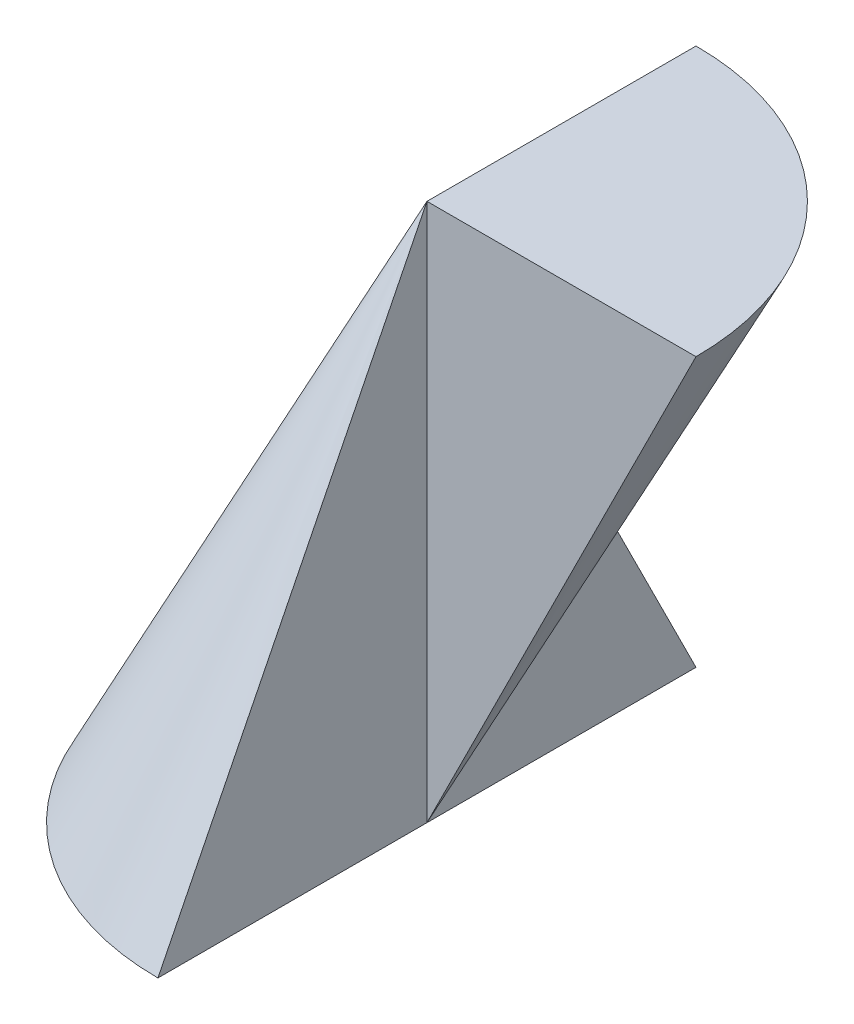
SolidWorks part; units mm, degrees
ref_plane "Front" through (0, 0, 0) normal (0, 0, 1) x (1, 0, 0)
ref_plane "Top" through (0, 0, 0) normal (0, 1, 0) x (1, 0, 0)
ref_plane "Right" through (0, 0, 0) normal (1, 0, 0) x (0, 0, -1)
sketch "Sketch1" plane through (0, 0, 0) normal (1, 0, 0) x (0, 0, -1)
  line L0 (0, 0) -> (2, 0)
  line L1 (2, 0) -> (0, 4)
  line L2 (0, 4) -> (0, 0)
  dimension "D1" = 4
  dimension "D2" = 2
revolve "Revolve1" add sketch "Sketch1" angle 180 about L2
sketch "Sketch2" plane through (0, 0, 0) normal (1, 0, 0) x (0, 0, -1)
  line L0 (0, 0) -> (2, 4)
  line L1 (2, 4) -> (0, 4)
  line L2 (0, 4) -> (0, 0)
  dimension "D1" = 2
revolve "Revolve2" add sketch "Sketch2" angle 90 about L2
